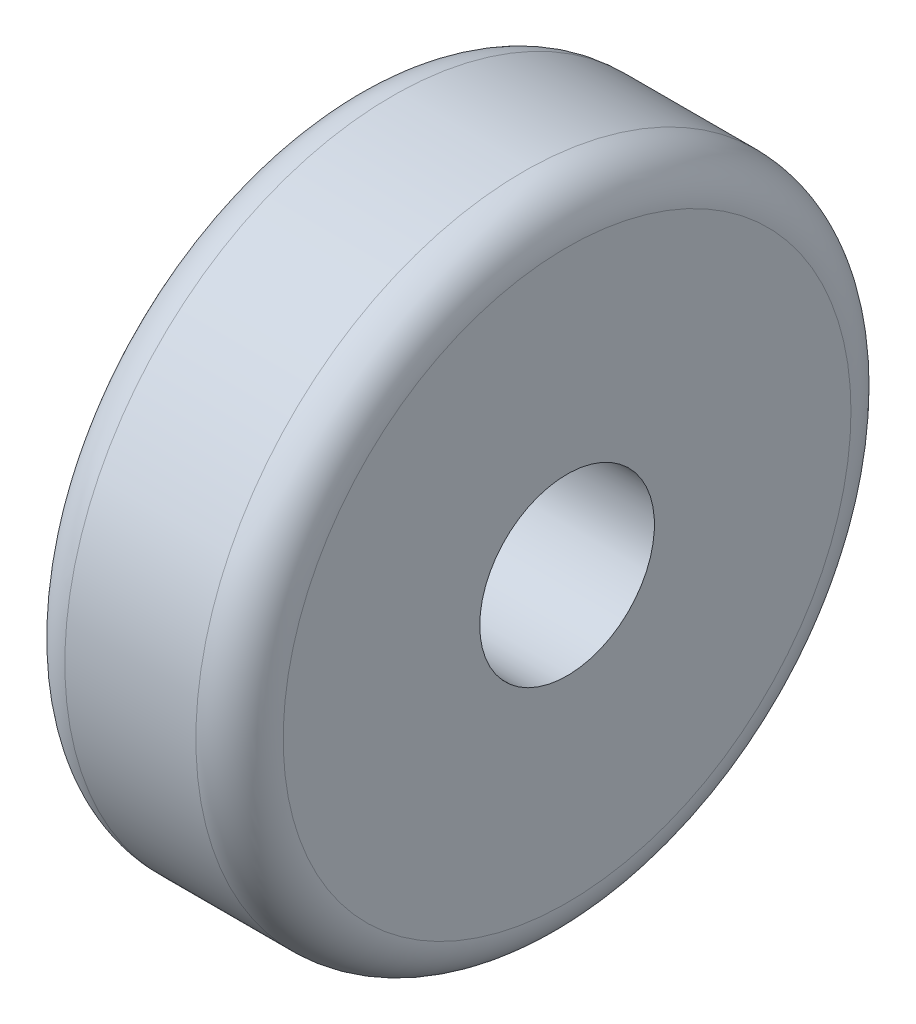
SolidWorks part; units mm, degrees
ref_plane "Front Plane" through (0, 0, 0) normal (0, 0, 1) x (1, 0, 0)
ref_plane "Top Plane" through (0, 0, 0) normal (0, 1, 0) x (1, 0, 0)
ref_plane "Right Plane" through (0, 0, 0) normal (1, 0, 0) x (0, 0, -1)
sketch "Sketch1" plane through (0, 0, 0) normal (1, 0, 0) x (0, 0, -1)
  circle A0 centre (0, 0) radius 150
extrude "Boss-Extrude1" add sketch "Sketch1" along normal blind 100
sketch "Sketch2" plane through (0, 0, 0) normal (-1, 0, 0) x (0, 0, 1)
  circle A0 centre (0, 0) radius 40
fillet "Fillet1" radius 20 2 edges at (0, 0, -150) (100, 0, -150)
extrude "Cut-Extrude1" cut sketch "Sketch2" against normal through all
equation "\"100..00mm\"=250"
